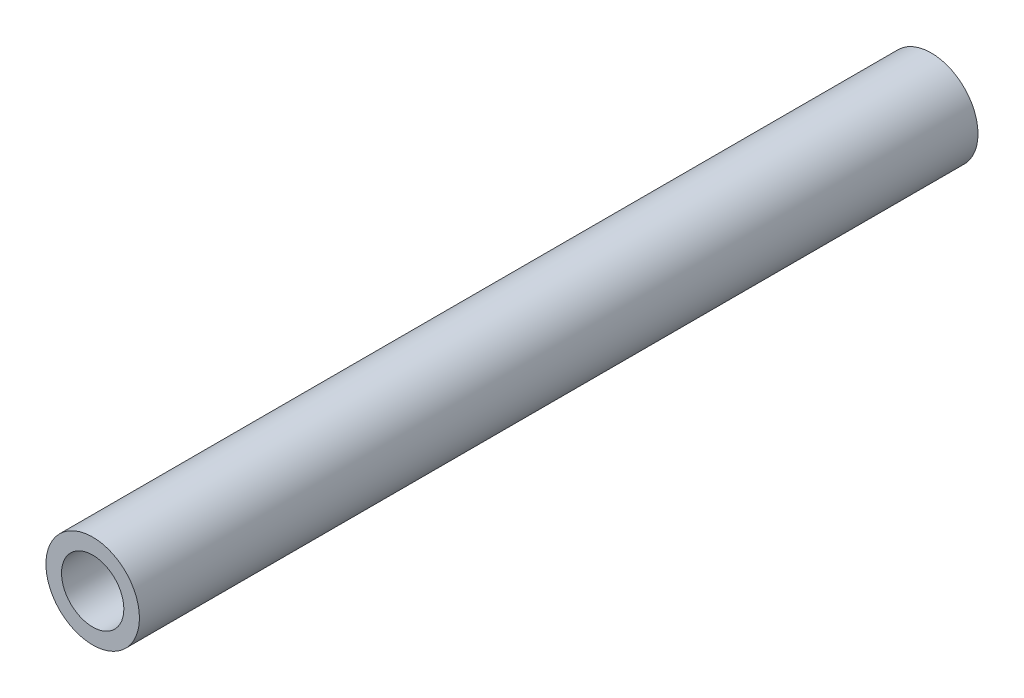
SolidWorks part; units mm, degrees
ref_plane "Front Plane" through (0, 0, 0) normal (0, 0, 1) x (1, 0, 0)
ref_plane "Top Plane" through (0, 0, 0) normal (0, 1, 0) x (1, 0, 0)
ref_plane "Right Plane" through (0, 0, 0) normal (1, 0, 0) x (0, 0, -1)
sketch "Sketch1" plane through (0, 0, 0) normal (0, 0, 1) x (1, 0, 0)
  circle A0 centre (0, 0) radius 7.62
  circle A2 centre (0, 0) radius 5.08
  dimension "D1" = 15.24
  dimension "D2" = 10.16
extrude "Boss-Extrude1" add sketch "Sketch1" along normal blind 136.652
